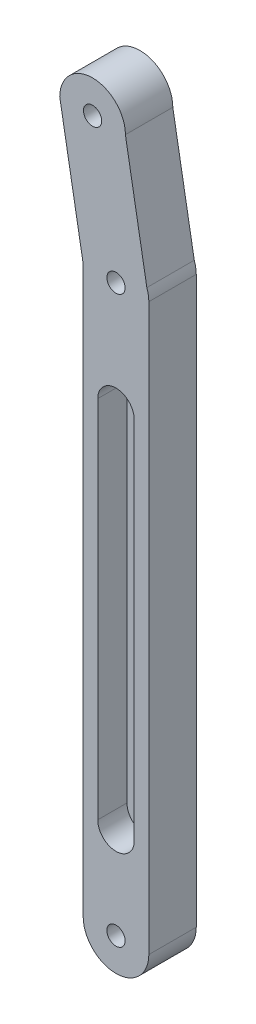
SolidWorks part; units mm, degrees
ref_plane "Front Plane" through (0, 0, 0) normal (0, 0, 1) x (1, 0, 0)
ref_plane "Top Plane" through (0, 0, 0) normal (0, 1, 0) x (1, 0, 0)
ref_plane "Right Plane" through (0, 0, 0) normal (1, 0, 0) x (0, 0, -1)
sketch "Sketch1" plane through (0, 0, 0) normal (0, 0, 1) x (1, 0, 0)
  line L0 (-14.3286, 112.6376) -> (-14.3286, -42.3624)
  line L1 (3.6714, -42.3624) -> (3.6714, 112.6376)
  line L4 (-20.7536, 149.0755) -> (-14.3286, 112.6376)
  line L5 (3.1286, 115.7158) -> (-2.7536, 149.0755)
  circle A0 centre (-5.3286, 112.6376) radius 2.5
  circle A1 centre (-5.3286, -42.3624) radius 2.5
  arc A2 (-14.3286, -42.3624) -> (3.6714, -42.3624) centre (-5.3286, -42.3624) ccw
  arc A3 (3.6714, 112.6376) -> (3.1286, 115.7158) centre (-5.3286, 112.6376) ccw
  circle A4 centre (-11.7536, 149.0755) radius 2.5
  arc A5 (-2.7536, 149.0755) -> (-20.7536, 149.0755) centre (-11.7536, 149.0755) ccw
  dimension "D2" = 18
  dimension "D3" = 18
  dimension "D4" = 5
  dimension "D5" = 5
  dimension "D8" = 5
  dimension "D9" = 18
  dimension "D1" = 155
  dimension "D7" = 37
extrude "Extrude1" add sketch "Sketch1" along normal blind 13
sketch "Sketch2" plane through (0, 0, 13) normal (0, 0, 1) x (1, 0, 0)
  line L0 (-14.3286, 112.6376) -> (-14.3286, -42.3624) construction
  line L1 (-0.3286, 82.6376) -> (-0.3286, -17.3624)
  line L2 (-10.3286, 82.6376) -> (-10.3286, -17.3624)
  arc A0 (-0.3286, 82.6376) -> (-10.3286, 82.6376) centre (-5.3286, 82.6376) ccw
  arc A1 (-10.3286, -17.3624) -> (-0.3286, -17.3624) centre (-5.3286, -17.3624) ccw
  circle A2 centre (-5.3286, -42.3624) radius 2.5 construction
  dimension "D1" = 10
  dimension "D2" = 10
  dimension "D3" = 9
  dimension "D4" = 9
  dimension "D5" = 100
  dimension "D6" = 25
extrude "Extrude2" cut sketch "Sketch2" against normal blind 8
